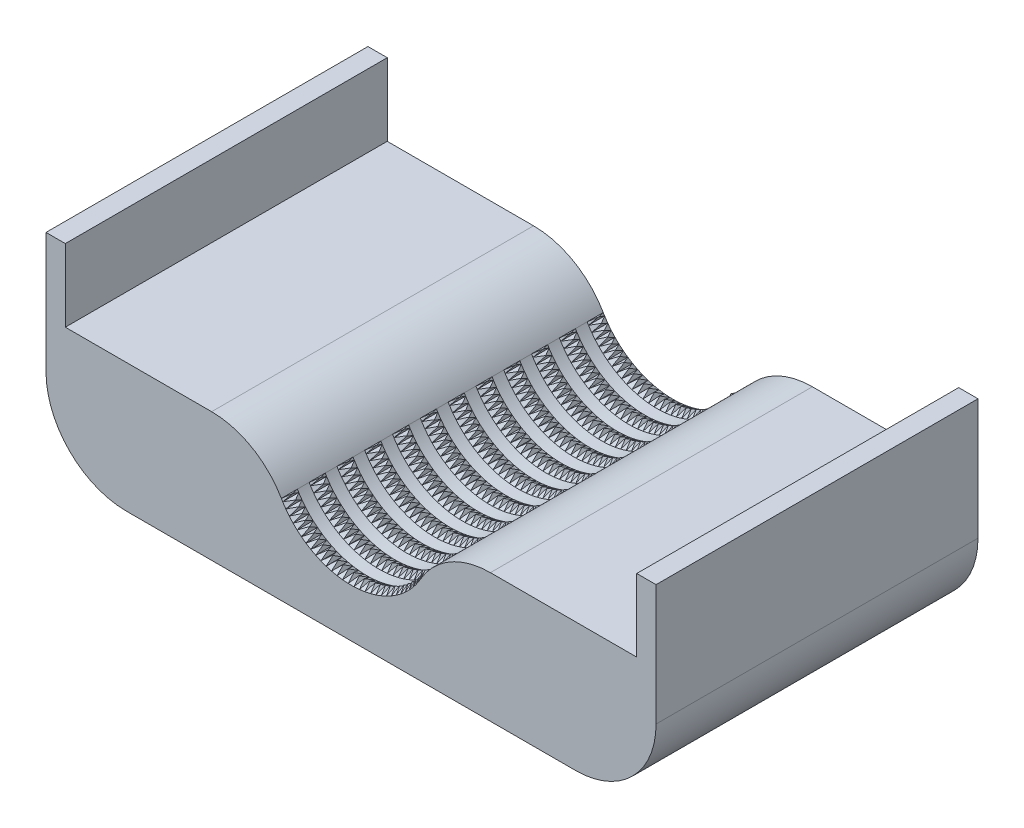
SolidWorks part; units mm, degrees
ref_plane "Front Plane" through (0, 0, 0) normal (0, 0, 1) x (1, 0, 0)
ref_plane "Top Plane" through (0, 0, 0) normal (0, 1, 0) x (1, 0, 0)
ref_plane "Right Plane" through (0, 0, 0) normal (1, 0, 0) x (0, 0, -1)
sketch "Sketch1" plane through (0, 0, 0) normal (0, 0, 1) x (1, 0, 0)
  line L0 (-17.3205, 0) -> (-35.5, 0)
  line L1 (-35.5, 0) -> (-35.5, 9)
  line L2 (-35.5, 9) -> (-37.9, 9)
  line L3 (-37.9, 9) -> (-37.9, -6)
  line L4 (-27.9, -16) -> (27.9, -16)
  line L5 (0, -16) -> (0, -10) construction
  line L6 (37.9, 9) -> (37.9, -6)
  line L7 (35.5, 9) -> (37.9, 9)
  line L8 (35.5, 0) -> (35.5, 9)
  line L9 (17.3205, 0) -> (35.5, 0)
  arc A0 (-8.6603, -5) -> (8.6603, -5) centre (0, 0) ccw
  arc A1 (-37.9, -6) -> (-27.9, -16) centre (-27.9, -6) ccw
  arc A2 (-17.3205, 0) -> (-8.6603, -5) centre (-17.3205, -10) cw
  arc A3 (37.9, -6) -> (27.9, -16) centre (27.9, -6) cw
  arc A4 (17.3205, 0) -> (8.6603, -5) centre (17.3205, -10) ccw
  point P11 (-37.9, -16)
  point P14 (-10, 0)
  dimension "D1" = 10
  dimension "D6" = 10
  dimension "D7" = 10
  dimension "D2" = 2.4
  dimension "D3" = 35.5
  dimension "D4" = 16
  dimension "D5" = 25
extrude "Boss-Extrude1" add sketch "Sketch1" along normal blind 40
sketch "Sketch2" plane through (0, 0, 0) normal (1, 0, 0) x (0, 0, -1)
  line L0 (-2, -10) -> (-1, -9.5)
  line L1 (-1, -9.5) -> (0, -10)
  line L2 (0, -10) -> (-2, -10)
  line L3 (-1, -9.5) -> (-1, -10) construction
  line L4 (-5.4545, -10) -> (-4.4545, -9.5)
  line L5 (-3.4545, -10) -> (-5.4545, -10)
  line L6 (-4.4545, -9.5) -> (-3.4545, -10)
  line L7 (-8.9091, -10) -> (-7.9091, -9.5)
  line L8 (-6.9091, -10) -> (-8.9091, -10)
  line L9 (-7.9091, -9.5) -> (-6.9091, -10)
  line L10 (-12.3636, -10) -> (-11.3636, -9.5)
  line L11 (-10.3636, -10) -> (-12.3636, -10)
  line L12 (-11.3636, -9.5) -> (-10.3636, -10)
  line L13 (-15.8182, -10) -> (-14.8182, -9.5)
  line L14 (-13.8182, -10) -> (-15.8182, -10)
  line L15 (-14.8182, -9.5) -> (-13.8182, -10)
  line L16 (-19.2727, -10) -> (-18.2727, -9.5)
  line L17 (-17.2727, -10) -> (-19.2727, -10)
  line L18 (-18.2727, -9.5) -> (-17.2727, -10)
  line L19 (-22.7273, -10) -> (-21.7273, -9.5)
  line L20 (-20.7273, -10) -> (-22.7273, -10)
  line L21 (-21.7273, -9.5) -> (-20.7273, -10)
  line L22 (-26.1818, -10) -> (-25.1818, -9.5)
  line L23 (-24.1818, -10) -> (-26.1818, -10)
  line L24 (-25.1818, -9.5) -> (-24.1818, -10)
  line L25 (-29.6364, -10) -> (-28.6364, -9.5)
  line L26 (-27.6364, -10) -> (-29.6364, -10)
  line L27 (-28.6364, -9.5) -> (-27.6364, -10)
  line L28 (-33.0909, -10) -> (-32.0909, -9.5)
  line L29 (-31.0909, -10) -> (-33.0909, -10)
  line L30 (-32.0909, -9.5) -> (-31.0909, -10)
  line L31 (-36.5455, -10) -> (-35.5455, -9.5)
  line L32 (-34.5455, -10) -> (-36.5455, -10)
  line L33 (-35.5455, -9.5) -> (-34.5455, -10)
  line L34 (-40, -10) -> (-39, -9.5)
  line L35 (-38, -10) -> (-40, -10)
  line L36 (-39, -9.5) -> (-38, -10)
  line L37 (-40, -5) -> (-40, -10) construction
  line L38 (0, 0) -> (50000, 0) construction
  dimension "D1" = 0.5
  dimension "D2" = 2
  dimension "D3" = 10
  dimension "D4" = 12
revolve "Revolve1" add sketch "Sketch2" angle 360 about L38
sketch "Sketch3" plane through (0, 0, 40) normal (0, 0, 1) x (1, 0, 0)
  line L0 (-8.6603, -5) -> (0, 0)
  line L1 (0, 0) -> (8.6603, -5)
  arc A0 (8.6603, -5) -> (-8.6603, -5) centre (0, 0) ccw
extrude "Cut-Extrude1" cut sketch "Sketch3" against normal through all
sketch "Sketch4" plane through (0, 0, 40) normal (0, 0, 1) x (1, 0, 0)
  line L0 (-8.2272, -4.75) -> (-8.49, -5.2839)
  line L1 (-8.49, -5.2839) -> (-7.895, -5.2839)
  line L2 (-8.49, -5.2839) -> (-8.0655, -5.0197) construction
  line L3 (-7.8752, -5.3133) -> (-8.1, -5.8643)
  line L4 (-8.1, -5.8643) -> (-7.5064, -5.8227)
  line L5 (-7.4846, -5.8506) -> (-7.6704, -6.416)
  line L6 (-7.6704, -6.416) -> (-7.0812, -6.333)
  line L7 (-7.0575, -6.3594) -> (-7.2033, -6.9363)
  line L8 (-7.2033, -6.9363) -> (-6.6213, -6.8124)
  line L9 (-6.5959, -6.837) -> (-6.701, -7.4227)
  line L10 (-6.701, -7.4227) -> (-6.1291, -7.2584)
  line L11 (-6.102, -7.2812) -> (-6.1659, -7.8728)
  line L12 (-6.1659, -7.8728) -> (-5.6069, -7.669)
  line L13 (-5.5782, -7.6898) -> (-5.6007, -8.2845)
  line L14 (-5.6007, -8.2845) -> (-5.0573, -8.042)
  line L15 (-5.0272, -8.0608) -> (-5.0081, -8.6556)
  line L16 (-5.0081, -8.6556) -> (-4.4829, -8.3758)
  line L17 (-4.4516, -8.3924) -> (-4.391, -8.9844)
  line L18 (-4.391, -8.9844) -> (-3.8867, -8.6686)
  line L19 (-3.8543, -8.683) -> (-3.7524, -9.2693)
  line L20 (-3.7524, -9.2693) -> (-3.2714, -8.919)
  line L21 (-3.2381, -8.9311) -> (-3.0955, -9.5088)
  line L22 (-3.0955, -9.5088) -> (-2.6401, -9.1258)
  line L23 (-2.6061, -9.1356) -> (-2.4234, -9.7019)
  line L24 (-2.4234, -9.7019) -> (-1.996, -9.288)
  line L25 (-1.9613, -9.2953) -> (-1.7395, -9.8475)
  line L26 (-1.7395, -9.8475) -> (-1.342, -9.4047)
  line L27 (-1.3069, -9.4097) -> (-1.0471, -9.945)
  line L28 (-1.0471, -9.945) -> (-0.6815, -9.4755)
  line L29 (-0.6462, -9.478) -> (-0.3496, -9.9939)
  line L30 (-0.3496, -9.9939) -> (-0.0177, -9.5)
  line L31 (0.0177, -9.5) -> (0.3496, -9.9939)
  line L32 (0.3496, -9.9939) -> (0.6462, -9.478)
  line L33 (0.6815, -9.4755) -> (1.0471, -9.945)
  line L34 (1.0471, -9.945) -> (1.3069, -9.4097)
  line L35 (1.342, -9.4047) -> (1.7395, -9.8475)
  line L36 (1.7395, -9.8475) -> (1.9613, -9.2953)
  line L37 (1.996, -9.288) -> (2.4234, -9.7019)
  line L38 (2.4234, -9.7019) -> (2.6061, -9.1356)
  line L39 (2.6401, -9.1258) -> (3.0955, -9.5088)
  line L40 (3.0955, -9.5088) -> (3.2381, -8.9311)
  line L41 (3.2714, -8.919) -> (3.7524, -9.2693)
  line L42 (3.7524, -9.2693) -> (3.8543, -8.683)
  line L43 (3.8867, -8.6686) -> (4.391, -8.9844)
  line L44 (4.391, -8.9844) -> (4.4516, -8.3924)
  line L45 (4.4829, -8.3758) -> (5.0081, -8.6556)
  line L46 (5.0081, -8.6556) -> (5.0272, -8.0608)
  line L47 (5.0573, -8.042) -> (5.6007, -8.2845)
  line L48 (5.6007, -8.2845) -> (5.5782, -7.6898)
  line L49 (5.6069, -7.669) -> (6.1659, -7.8728)
  line L50 (6.1659, -7.8728) -> (6.102, -7.2812)
  line L51 (6.1291, -7.2584) -> (6.701, -7.4227)
  line L52 (6.701, -7.4227) -> (6.5959, -6.837)
  line L53 (6.6213, -6.8124) -> (7.2033, -6.9363)
  line L54 (7.2033, -6.9363) -> (7.0575, -6.3594)
  line L55 (7.0812, -6.333) -> (7.6704, -6.416)
  line L56 (7.6704, -6.416) -> (7.4846, -5.8506)
  line L57 (7.5064, -5.8227) -> (8.1, -5.8643)
  line L58 (8.1, -5.8643) -> (7.8752, -5.3133)
  line L59 (7.895, -5.2839) -> (8.49, -5.2839)
  line L60 (8.49, -5.2839) -> (8.2272, -4.75)
  line L61 (8.2449, -4.7193) -> (8.8385, -4.6777)
  line L62 (8.8385, -4.6777) -> (8.5391, -4.1635)
  line L63 (8.2272, -4.75) -> (8.6603, -5) construction
  arc A0 (-8.6603, -5) -> (8.6603, -5) centre (0, 0) ccw construction
  arc A1 (-8.2272, -4.75) -> (-7.895, -5.2839) centre (0, 0) ccw
  circle A2 centre (0, 0) radius 10 construction
  arc A3 (-7.8752, -5.3133) -> (-7.5064, -5.8227) centre (0, 0) ccw
  arc A4 (-7.4846, -5.8506) -> (-7.0812, -6.333) centre (0, 0) ccw
  arc A5 (-7.0575, -6.3594) -> (-6.6213, -6.8124) centre (0, 0) ccw
  arc A6 (-6.5959, -6.837) -> (-6.1291, -7.2584) centre (0, 0) ccw
  arc A7 (-6.102, -7.2812) -> (-5.6069, -7.669) centre (0, 0) ccw
  arc A8 (-5.5782, -7.6898) -> (-5.0573, -8.042) centre (0, 0) ccw
  arc A9 (-5.0272, -8.0608) -> (-4.4829, -8.3758) centre (0, 0) ccw
  arc A10 (-4.4516, -8.3924) -> (-3.8867, -8.6686) centre (0, 0) ccw
  arc A11 (-3.8543, -8.683) -> (-3.2714, -8.919) centre (0, 0) ccw
  arc A12 (-3.2381, -8.9311) -> (-2.6401, -9.1258) centre (0, 0) ccw
  arc A13 (-2.6061, -9.1356) -> (-1.996, -9.288) centre (0, 0) ccw
  arc A14 (-1.9613, -9.2953) -> (-1.342, -9.4047) centre (0, 0) ccw
  arc A15 (-1.3069, -9.4097) -> (-0.6815, -9.4755) centre (0, 0) ccw
  arc A16 (-0.6462, -9.478) -> (-0.0177, -9.5) centre (0, 0) ccw
  arc A17 (0.0177, -9.5) -> (0.6462, -9.478) centre (0, 0) ccw
  arc A18 (0.6815, -9.4755) -> (1.3069, -9.4097) centre (0, 0) ccw
  arc A19 (1.342, -9.4047) -> (1.9613, -9.2953) centre (0, 0) ccw
  arc A20 (1.996, -9.288) -> (2.6061, -9.1356) centre (0, 0) ccw
  arc A21 (2.6401, -9.1258) -> (3.2381, -8.9311) centre (0, 0) ccw
  arc A22 (3.2714, -8.919) -> (3.8543, -8.683) centre (0, 0) ccw
  arc A23 (3.8867, -8.6686) -> (4.4516, -8.3924) centre (0, 0) ccw
  arc A24 (4.4829, -8.3758) -> (5.0272, -8.0608) centre (0, 0) ccw
  arc A25 (5.0573, -8.042) -> (5.5782, -7.6898) centre (0, 0) ccw
  arc A26 (5.6069, -7.669) -> (6.102, -7.2812) centre (0, 0) ccw
  arc A27 (6.1291, -7.2584) -> (6.5959, -6.837) centre (0, 0) ccw
  arc A28 (6.6213, -6.8124) -> (7.0575, -6.3594) centre (0, 0) ccw
  arc A29 (7.0812, -6.333) -> (7.4846, -5.8506) centre (0, 0) ccw
  arc A30 (7.5064, -5.8227) -> (7.8752, -5.3133) centre (0, 0) ccw
  arc A31 (7.895, -5.2839) -> (8.2272, -4.75) centre (0, 0) ccw
  arc A32 (8.2449, -4.7193) -> (8.5391, -4.1635) centre (0, 0) ccw
  point P105 (0, 0)
  dimension "D1" = 31
extrude "Cut-Extrude2" cut sketch "Sketch4" against normal through all
